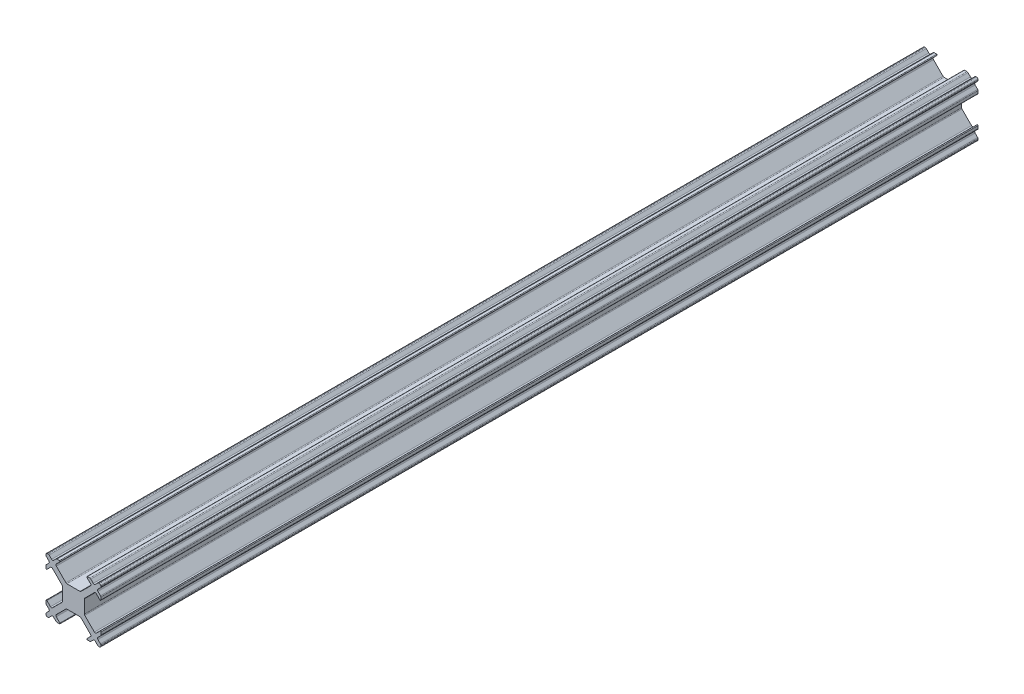
SolidWorks part; units mm, degrees
ref_plane "Front Plane" through (0, 0, 0) normal (0, 0, 1) x (1, 0, 0)
ref_plane "Top Plane" through (0, 0, 0) normal (0, 1, 0) x (1, 0, 0)
ref_plane "Right Plane" through (0, 0, 0) normal (1, 0, 0) x (0, 0, -1)
sketch "Sketch1" plane through (0, 0, 0) normal (0, 0, 1) x (1, 0, 0)
  line L0 (-26.4346, 28.4965) -> (-25.9796, 28.9515)
  line L1 (-25.1311, 29.8) -> (-24.676, 30.2551)
  line L2 (-24.676, 20.4015) -> (-25.1311, 20.8565)
  line L3 (-25.9796, 21.7051) -> (-26.4346, 22.1601)
  line L4 (-26.5078, 30.0783) -> (-26.5078, 29.9369)
  line L5 (-26.5078, 28.3197) -> (-26.5078, 27.8626)
  line L6 (-26.5078, 22.794) -> (-26.5078, 22.3369)
  line L7 (-26.5078, 20.7197) -> (-26.5078, 20.5783)
  line L8 (-23.9714, 30.1576) -> (-24.624, 29.5051)
  line L9 (-25.6846, 28.4444) -> (-26.3371, 27.7919)
  line L10 (-26.2578, 20.3283) -> (-26.1164, 20.3283)
  line L11 (-24.4993, 20.3283) -> (-24.0422, 20.3283)
  line L12 (-18.9735, 20.3283) -> (-18.5164, 20.3283)
  line L13 (-16.8993, 20.3283) -> (-16.7578, 20.3283)
  line L14 (-26.3371, 22.8647) -> (-25.6846, 22.2122)
  line L15 (-24.624, 21.1515) -> (-23.9714, 20.499)
  line L16 (-23.5078, 26.5176) -> (-23.5078, 24.139)
  line L17 (-22.6972, 23.3283) -> (-20.3185, 23.3283)
  line L18 (-25.3311, 22.2122) -> (-23.5811, 23.9622)
  line L19 (-20.1417, 27.4015) -> (-18.3917, 29.1515)
  line L20 (-18.3917, 21.5051) -> (-20.1417, 23.2551)
  line L21 (-23.5811, 26.6944) -> (-25.3311, 28.4444)
  line L22 (-26.4346, 20.8965) -> (-25.9796, 21.3515)
  line L23 (-17.5311, 29.8) -> (-17.076, 30.2551)
  line L24 (-17.076, 20.4015) -> (-17.5311, 20.8565)
  line L25 (-25.9796, 29.3051) -> (-26.4346, 29.7601)
  line L26 (-16.5811, 29.7601) -> (-17.0361, 29.3051)
  line L27 (-25.4846, 20.8565) -> (-25.9396, 20.4015)
  line L28 (-17.6846, 28.4444) -> (-19.4346, 26.6944)
  line L29 (-22.874, 23.2551) -> (-24.624, 21.5051)
  line L30 (-25.9396, 30.2551) -> (-25.4846, 29.8)
  line L31 (-17.0361, 21.3515) -> (-16.5811, 20.8965)
  line L32 (-24.624, 29.1515) -> (-22.874, 27.4015)
  line L33 (-19.4346, 23.9622) -> (-17.6846, 22.2122)
  line L34 (-19.5078, 24.139) -> (-19.5078, 26.5176)
  line L35 (-20.3185, 27.3283) -> (-22.6972, 27.3283)
  line L36 (-16.5078, 20.5783) -> (-16.5078, 20.7197)
  line L37 (-16.5078, 22.3369) -> (-16.5078, 22.794)
  line L38 (-16.5078, 27.8626) -> (-16.5078, 28.3197)
  line L39 (-16.5078, 29.9369) -> (-16.5078, 30.0783)
  line L40 (-16.7578, 30.3283) -> (-16.8993, 30.3283)
  line L41 (-18.5164, 30.3283) -> (-18.9735, 30.3283)
  line L42 (-24.0422, 30.3283) -> (-24.4993, 30.3283)
  line L43 (-26.1164, 30.3283) -> (-26.2578, 30.3283)
  line L44 (-19.0442, 20.499) -> (-18.3917, 21.1515)
  line L45 (-17.3311, 22.2122) -> (-16.6786, 22.8647)
  line L46 (-16.6786, 27.7919) -> (-17.3311, 28.4444)
  line L47 (-18.3917, 29.5051) -> (-19.0442, 30.1576)
  line L48 (-16.5811, 22.1601) -> (-17.0361, 21.7051)
  line L49 (-17.8846, 20.8565) -> (-18.3396, 20.4015)
  line L50 (-18.3396, 30.2551) -> (-17.8846, 29.8)
  line L51 (-17.0361, 28.9515) -> (-16.5811, 28.4965)
  arc A0 (-16.5078, 30.0783) -> (-16.7578, 30.3283) centre (-16.7578, 30.0783) ccw
  arc A1 (-26.2578, 30.3283) -> (-26.5078, 30.0783) centre (-26.2578, 30.0783) ccw
  arc A2 (-16.7578, 20.3283) -> (-16.5078, 20.5783) centre (-16.7578, 20.5783) ccw
  arc A3 (-26.5078, 20.5783) -> (-26.2578, 20.3283) centre (-26.2578, 20.5783) ccw
  arc A4 (-18.9735, 30.3283) -> (-19.0442, 30.1576) centre (-18.9735, 30.2283) ccw
  arc A5 (-16.6786, 27.7919) -> (-16.5078, 27.8626) centre (-16.6078, 27.8626) ccw
  arc A6 (-16.5078, 22.794) -> (-16.6786, 22.8647) centre (-16.6078, 22.794) ccw
  arc A7 (-19.0442, 20.499) -> (-18.9735, 20.3283) centre (-18.9735, 20.4283) ccw
  arc A8 (-26.3371, 22.8647) -> (-26.5078, 22.794) centre (-26.4078, 22.794) ccw
  arc A9 (-26.5078, 27.8626) -> (-26.3371, 27.7919) centre (-26.4078, 27.8626) ccw
  arc A10 (-23.9714, 30.1576) -> (-24.0422, 30.3283) centre (-24.0422, 30.2283) ccw
  arc A11 (-24.0422, 20.3283) -> (-23.9714, 20.499) centre (-24.0422, 20.4283) ccw
  arc A12 (-22.874, 27.4015) -> (-22.6972, 27.3283) centre (-22.6972, 27.5783) ccw
  arc A13 (-20.3185, 27.3283) -> (-20.1417, 27.4015) centre (-20.3185, 27.5783) ccw
  arc A14 (-19.5078, 24.139) -> (-19.4346, 23.9622) centre (-19.2578, 24.139) ccw
  arc A15 (-17.6846, 22.2122) -> (-17.3311, 22.2122) centre (-17.5078, 22.389) ccw
  arc A16 (-22.6972, 23.3283) -> (-22.874, 23.2551) centre (-22.6972, 23.0783) ccw
  arc A17 (-20.1417, 23.2551) -> (-20.3185, 23.3283) centre (-20.3185, 23.0783) ccw
  arc A18 (-25.3311, 28.4444) -> (-25.6846, 28.4444) centre (-25.5078, 28.2676) ccw
  arc A19 (-23.5811, 23.9622) -> (-23.5078, 24.139) centre (-23.7578, 24.139) ccw
  arc A20 (-23.5078, 26.5176) -> (-23.5811, 26.6944) centre (-23.7578, 26.5176) ccw
  arc A21 (-25.6846, 22.2122) -> (-25.3311, 22.2122) centre (-25.5078, 22.389) ccw
  arc A22 (-24.624, 21.5051) -> (-24.624, 21.1515) centre (-24.4472, 21.3283) ccw
  arc A23 (-18.3917, 21.1515) -> (-18.3917, 21.5051) centre (-18.5685, 21.3283) ccw
  arc A24 (-18.3917, 29.1515) -> (-18.3917, 29.5051) centre (-18.5685, 29.3283) ccw
  arc A25 (-17.3311, 28.4444) -> (-17.6846, 28.4444) centre (-17.5078, 28.2676) ccw
  arc A26 (-19.4346, 26.6944) -> (-19.5078, 26.5176) centre (-19.2578, 26.5176) ccw
  arc A27 (-24.624, 29.5051) -> (-24.624, 29.1515) centre (-24.4472, 29.3283) ccw
  arc A28 (-17.0361, 29.3051) -> (-17.0361, 28.9515) centre (-16.8593, 29.1283) ccw
  arc A29 (-17.0361, 21.7051) -> (-17.0361, 21.3515) centre (-16.8593, 21.5283) ccw
  arc A30 (-25.4846, 29.8) -> (-25.1311, 29.8) centre (-25.3078, 29.9768) ccw
  arc A31 (-17.8846, 29.8) -> (-17.5311, 29.8) centre (-17.7078, 29.9768) ccw
  arc A32 (-25.9796, 28.9515) -> (-25.9796, 29.3051) centre (-26.1564, 29.1283) ccw
  arc A33 (-25.9796, 21.3515) -> (-25.9796, 21.7051) centre (-26.1564, 21.5283) ccw
  arc A34 (-17.5311, 20.8565) -> (-17.8846, 20.8565) centre (-17.7078, 20.6798) ccw
  arc A35 (-25.1311, 20.8565) -> (-25.4846, 20.8565) centre (-25.3078, 20.6798) ccw
  arc A36 (-18.3396, 30.2551) -> (-18.5164, 30.3283) centre (-18.5164, 30.0783) ccw
  arc A37 (-16.8993, 30.3283) -> (-17.076, 30.2551) centre (-16.8993, 30.0783) ccw
  arc A38 (-24.4993, 30.3283) -> (-24.676, 30.2551) centre (-24.4993, 30.0783) ccw
  arc A39 (-25.9396, 30.2551) -> (-26.1164, 30.3283) centre (-26.1164, 30.0783) ccw
  arc A40 (-26.5078, 29.9369) -> (-26.4346, 29.7601) centre (-26.2578, 29.9369) ccw
  arc A41 (-26.4346, 28.4965) -> (-26.5078, 28.3197) centre (-26.2578, 28.3197) ccw
  arc A42 (-26.4346, 20.8965) -> (-26.5078, 20.7197) centre (-26.2578, 20.7197) ccw
  arc A43 (-26.5078, 22.3369) -> (-26.4346, 22.1601) centre (-26.2578, 22.3369) ccw
  arc A44 (-24.676, 20.4015) -> (-24.4993, 20.3283) centre (-24.4993, 20.5783) ccw
  arc A45 (-18.5164, 20.3283) -> (-18.3396, 20.4015) centre (-18.5164, 20.5783) ccw
  arc A46 (-17.076, 20.4015) -> (-16.8993, 20.3283) centre (-16.8993, 20.5783) ccw
  arc A47 (-16.5078, 28.3197) -> (-16.5811, 28.4965) centre (-16.7578, 28.3197) ccw
  arc A48 (-16.5078, 20.7197) -> (-16.5811, 20.8965) centre (-16.7578, 20.7197) ccw
  arc A49 (-16.5811, 22.1601) -> (-16.5078, 22.3369) centre (-16.7578, 22.3369) ccw
  arc A50 (-16.5811, 29.7601) -> (-16.5078, 29.9369) centre (-16.7578, 29.9369) ccw
  arc A51 (-26.1164, 20.3283) -> (-25.9396, 20.4015) centre (-26.1164, 20.5783) ccw
  dimension "D1" = 4
  dimension "D2" = 10
extrude "Boss-Extrude1" add sketch "Sketch1" along normal blind 160
